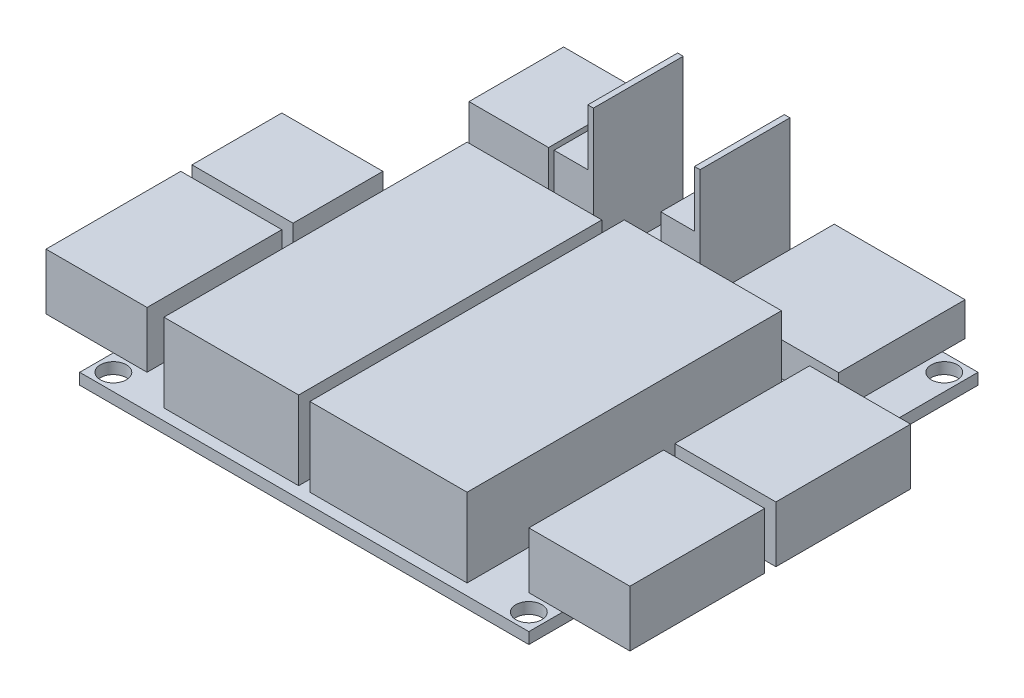
SolidWorks part; units mm, degrees
ref_plane "Front Plane" through (0, 0, 0) normal (0, 0, 1) x (1, 0, 0)
ref_plane "Top Plane" through (0, 0, 0) normal (0, 1, 0) x (1, 0, 0)
ref_plane "Right Plane" through (0, 0, 0) normal (1, 0, 0) x (0, 0, -1)
sketch "pcb layout" plane through (0, 0, 0) normal (0, 1, 0) x (1, 0, 0)
  line L0 (0, 0) -> (0, 50.8)
  line L1 (0, 50.8) -> (50.8, 50.8)
  line L2 (50.8, 50.8) -> (50.8, 0)
  line L3 (50.8, 0) -> (0, 0)
  line L4 (13.97, 38.1) -> (13.97, 36.83)
  line L5 (11.43, 38.735) -> (16.51, 38.735)
  line L6 (16.51, 38.735) -> (16.51, 36.195)
  line L7 (16.51, 36.195) -> (11.43, 36.195)
  line L8 (11.43, 36.195) -> (11.43, 38.735)
  line L9 (21.59, 44.45) -> (21.59, 45.72)
  line L10 (24.13, 43.815) -> (19.05, 43.815)
  line L11 (19.05, 43.815) -> (19.05, 46.355)
  line L12 (19.05, 46.355) -> (24.13, 46.355)
  line L13 (24.13, 46.355) -> (24.13, 43.815)
  line L14 (21.59, 47.625) -> (21.59, 48.895)
  line L15 (24.13, 46.99) -> (19.05, 46.99)
  line L16 (19.05, 46.99) -> (19.05, 49.53)
  line L17 (19.05, 49.53) -> (24.13, 49.53)
  line L18 (24.13, 49.53) -> (24.13, 46.99)
  line L19 (21.59, 40.3225) -> (21.59, 41.5925)
  line L20 (24.13, 39.6875) -> (19.05, 39.6875)
  line L21 (19.05, 39.6875) -> (19.05, 42.2275)
  line L22 (19.05, 42.2275) -> (24.13, 42.2275)
  line L23 (24.13, 42.2275) -> (24.13, 39.6875)
  line L24 (21.59, 37.1475) -> (21.59, 38.4175)
  line L25 (24.13, 36.5125) -> (19.05, 36.5125)
  line L26 (19.05, 36.5125) -> (19.05, 39.0525)
  line L27 (19.05, 39.0525) -> (24.13, 39.0525)
  line L28 (24.13, 39.0525) -> (24.13, 36.5125)
  line L29 (13.208, 35.56) -> (17.272, 35.56)
  line L30 (13.208, 35.56) -> (13.208, 33.02)
  line L31 (17.272, 33.02) -> (13.208, 33.02)
  line L32 (17.272, 33.02) -> (17.272, 35.56)
  line L33 (15.875, 34.29) -> (15.24, 34.29)
  line L34 (14.224, 33.655) -> (14.224, 34.925)
  line L35 (14.224, 34.925) -> (15.24, 34.29)
  line L36 (15.24, 34.29) -> (13.716, 34.29)
  line L37 (15.24, 34.29) -> (14.224, 33.655)
  line L38 (15.24, 33.655) -> (15.24, 34.29)
  line L39 (15.24, 34.29) -> (15.24, 34.925)
  line L40 (4.39, 39.64) -> (6.49, 39.64)
  line L41 (4.39, 50.34) -> (4.39, 45.04)
  line L42 (4.39, 39.64) -> (4.39, 40.34)
  line L43 (13.39, 50.34) -> (13.39, 39.64)
  line L44 (13.39, 39.64) -> (11.29, 39.64)
  line L45 (13.39, 50.34) -> (4.39, 50.34)
  line L46 (8.255, 1.27) -> (23.495, 1.27)
  line L47 (23.495, 1.27) -> (23.495, 35.56)
  line L48 (23.495, 35.56) -> (8.255, 35.56)
  line L49 (8.255, 35.56) -> (8.255, 1.27)
  line L50 (12.2936, 3.8354) -> (11.7343, 3.8354)
  line L51 (11.7343, 3.8354) -> (11.7343, 4.115)
  line L52 (11.7343, 4.115) -> (11.8275, 4.2082)
  line L53 (11.8275, 4.2082) -> (12.014, 4.2082)
  line L54 (12.014, 4.2082) -> (12.1072, 4.115)
  line L55 (12.1072, 4.115) -> (12.1072, 3.8354)
  line L56 (12.1072, 4.0218) -> (12.2936, 4.2082)
  line L57 (11.7343, 4.3967) -> (12.2936, 4.7696)
  line L58 (11.7343, 4.7696) -> (12.2936, 4.3967)
  line L59 (14.8336, 4.0218) -> (14.2743, 4.0218)
  line L60 (14.2743, 3.8354) -> (14.2743, 4.2082)
  line L61 (14.2743, 4.3967) -> (14.8336, 4.7696)
  line L62 (14.2743, 4.7696) -> (14.8336, 4.3967)
  line L63 (16.9075, 4.2082) -> (16.8143, 4.115)
  line L64 (16.8143, 4.115) -> (16.8143, 3.9286)
  line L65 (16.8143, 3.9286) -> (16.9075, 3.8354)
  line L66 (16.9075, 3.8354) -> (17.2804, 3.8354)
  line L67 (17.2804, 3.8354) -> (17.3736, 3.9286)
  line L68 (17.3736, 3.9286) -> (17.3736, 4.115)
  line L69 (17.3736, 4.115) -> (17.2804, 4.2082)
  line L70 (17.2804, 4.2082) -> (17.094, 4.2082)
  line L71 (17.094, 4.2082) -> (17.094, 4.0218)
  line L72 (17.3736, 4.3967) -> (16.8143, 4.3967)
  line L73 (16.8143, 4.3967) -> (17.3736, 4.7696)
  line L74 (17.3736, 4.7696) -> (16.8143, 4.7696)
  line L75 (16.8143, 4.958) -> (17.3736, 4.958)
  line L76 (17.3736, 4.958) -> (17.3736, 5.2377)
  line L77 (17.3736, 5.2377) -> (17.2804, 5.3309)
  line L78 (17.2804, 5.3309) -> (16.9075, 5.3309)
  line L79 (16.9075, 5.3309) -> (16.8143, 5.2377)
  line L80 (16.8143, 5.2377) -> (16.8143, 4.958)
  line L81 (19.3543, 3.8354) -> (19.7272, 3.8354)
  line L82 (19.7272, 3.8354) -> (19.9136, 4.0218)
  line L83 (19.9136, 4.0218) -> (19.7272, 4.2082)
  line L84 (19.7272, 4.2082) -> (19.3543, 4.2082)
  line L85 (19.4475, 4.7696) -> (19.3543, 4.6763)
  line L86 (19.3543, 4.6763) -> (19.3543, 4.4899)
  line L87 (19.3543, 4.4899) -> (19.4475, 4.3967)
  line L88 (19.4475, 4.3967) -> (19.8204, 4.3967)
  line L89 (19.8204, 4.3967) -> (19.9136, 4.4899)
  line L90 (19.9136, 4.4899) -> (19.9136, 4.6763)
  line L91 (19.9136, 4.6763) -> (19.8204, 4.7696)
  line L92 (19.4475, 5.3309) -> (19.3543, 5.2377)
  line L93 (19.3543, 5.2377) -> (19.3543, 5.0512)
  line L94 (19.3543, 5.0512) -> (19.4475, 4.958)
  line L95 (19.4475, 4.958) -> (19.8204, 4.958)
  line L96 (19.8204, 4.958) -> (19.9136, 5.0512)
  line L97 (19.9136, 5.0512) -> (19.9136, 5.2377)
  line L98 (19.9136, 5.2377) -> (19.8204, 5.3309)
  line L99 (21.8943, 3.8354) -> (22.4536, 3.8354)
  line L100 (22.2672, 3.8354) -> (21.8943, 4.2082)
  line L101 (22.174, 3.9286) -> (22.4536, 4.2082)
  line L102 (21.8943, 4.7696) -> (21.8943, 4.3967)
  line L103 (21.8943, 4.3967) -> (22.4536, 4.3967)
  line L104 (22.4536, 4.3967) -> (22.4536, 4.7696)
  line L105 (22.174, 4.3967) -> (22.174, 4.5831)
  line L106 (21.8943, 4.958) -> (21.9875, 4.958)
  line L107 (21.9875, 4.958) -> (22.174, 5.1444)
  line L108 (22.174, 5.1444) -> (21.9875, 5.3309)
  line L109 (21.9875, 5.3309) -> (21.8943, 5.3309)
  line L110 (22.174, 5.1444) -> (22.4536, 5.1444)
  line L111 (9.2875, 4.2082) -> (9.1943, 4.115)
  line L112 (9.1943, 4.115) -> (9.1943, 3.9286)
  line L113 (9.1943, 3.9286) -> (9.2875, 3.8354)
  line L114 (9.2875, 3.8354) -> (9.3808, 3.8354)
  line L115 (9.3808, 3.8354) -> (9.474, 3.9286)
  line L116 (9.474, 3.9286) -> (9.474, 4.115)
  line L117 (9.474, 4.115) -> (9.5672, 4.2082)
  line L118 (9.5672, 4.2082) -> (9.6604, 4.2082)
  line L119 (9.6604, 4.2082) -> (9.7536, 4.115)
  line L120 (9.7536, 4.115) -> (9.7536, 3.9286)
  line L121 (9.7536, 3.9286) -> (9.6604, 3.8354)
  line L122 (9.7536, 4.5831) -> (9.1943, 4.5831)
  line L123 (9.1943, 4.3967) -> (9.1943, 4.7696)
  line L124 (9.7536, 4.958) -> (9.3808, 4.958)
  line L125 (9.3808, 4.958) -> (9.1943, 5.1444)
  line L126 (9.1943, 5.1444) -> (9.3808, 5.3309)
  line L127 (9.3808, 5.3309) -> (9.7536, 5.3309)
  line L128 (9.474, 4.958) -> (9.474, 5.3309)
  line L129 (9.7536, 5.7058) -> (9.1943, 5.7058)
  line L130 (9.1943, 5.5193) -> (9.1943, 5.8922)
  line L131 (9.1943, 6.4535) -> (9.1943, 6.0806)
  line L132 (9.1943, 6.0806) -> (9.7536, 6.0806)
  line L133 (9.7536, 6.0806) -> (9.7536, 6.4535)
  line L134 (9.474, 6.0806) -> (9.474, 6.2671)
  line L135 (7.62, 36.5125) -> (7.62, 32.0675)
  line L136 (7.62, 32.0675) -> (5.715, 32.0675)
  line L137 (5.715, 32.0675) -> (5.715, 36.5125)
  line L138 (5.715, 36.5125) -> (7.62, 36.5125)
  line L139 (12.7, 32.512) -> (17.78, 32.512)
  line L140 (17.78, 32.512) -> (17.78, 31.75)
  line L141 (17.78, 31.75) -> (17.78, 30.988)
  line L142 (17.78, 30.988) -> (12.7, 30.988)
  line L143 (12.7, 30.988) -> (12.7, 31.75)
  line L144 (12.7, 31.75) -> (12.7, 32.512)
  line L145 (17.78, 31.75) -> (18.034, 31.75)
  line L146 (12.7, 31.75) -> (12.446, 31.75)
  line L147 (13.2842, 32.0214) -> (13.5723, 32.3095)
  line L148 (13.5723, 32.3095) -> (13.5723, 31.4452)
  line L149 (13.2842, 31.4452) -> (13.8604, 31.4452)
  line L150 (14.2197, 31.4452) -> (14.2197, 31.5893)
  line L151 (14.2197, 31.5893) -> (14.3638, 31.5893)
  line L152 (14.3638, 31.5893) -> (14.3638, 31.4452)
  line L153 (14.3638, 31.4452) -> (14.2197, 31.4452)
  line L154 (14.6875, 32.0214) -> (14.9756, 32.3095)
  line L155 (14.9756, 32.3095) -> (14.9756, 31.4452)
  line L156 (14.6875, 31.4452) -> (15.2637, 31.4452)
  line L157 (15.623, 32.3095) -> (15.623, 31.4452)
  line L158 (15.623, 31.7333) -> (16.1992, 32.3095)
  line L159 (15.7671, 31.8774) -> (16.1992, 31.4452)
  line L160 (16.5585, 31.4452) -> (16.7026, 31.4452)
  line L161 (16.7026, 31.4452) -> (16.7026, 31.7333)
  line L162 (16.7026, 31.7333) -> (16.5585, 31.8774)
  line L163 (16.5585, 31.8774) -> (16.5585, 32.1655)
  line L164 (16.5585, 32.1655) -> (16.7026, 32.3095)
  line L165 (16.7026, 32.3095) -> (16.9907, 32.3095)
  line L166 (16.9907, 32.3095) -> (17.1347, 32.1655)
  line L167 (17.1347, 32.1655) -> (17.1347, 31.8774)
  line L168 (17.1347, 31.8774) -> (16.9907, 31.7333)
  line L169 (16.9907, 31.7333) -> (16.9907, 31.4452)
  line L170 (16.9907, 31.4452) -> (17.1347, 31.4452)
  line L171 (12.7, 12.192) -> (17.78, 12.192)
  line L172 (17.78, 12.192) -> (17.78, 11.43)
  line L173 (17.78, 11.43) -> (17.78, 10.668)
  line L174 (17.78, 10.668) -> (12.7, 10.668)
  line L175 (12.7, 10.668) -> (12.7, 11.43)
  line L176 (12.7, 11.43) -> (12.7, 12.192)
  line L177 (17.78, 11.43) -> (18.034, 11.43)
  line L178 (12.7, 11.43) -> (12.446, 11.43)
  line L179 (13.2842, 11.7014) -> (13.5723, 11.9895)
  line L180 (13.5723, 11.9895) -> (13.5723, 11.1252)
  line L181 (13.2842, 11.1252) -> (13.8604, 11.1252)
  line L182 (14.2197, 11.2693) -> (14.2197, 11.8455)
  line L183 (14.2197, 11.8455) -> (14.3638, 11.9895)
  line L184 (14.3638, 11.9895) -> (14.6519, 11.9895)
  line L185 (14.6519, 11.9895) -> (14.7959, 11.8455)
  line L186 (14.7959, 11.8455) -> (14.7959, 11.2693)
  line L187 (14.7959, 11.2693) -> (14.6519, 11.1252)
  line L188 (14.6519, 11.1252) -> (14.3638, 11.1252)
  line L189 (14.3638, 11.1252) -> (14.2197, 11.2693)
  line L190 (14.2197, 11.2693) -> (14.7959, 11.8455)
  line L191 (15.1552, 11.9895) -> (15.1552, 11.1252)
  line L192 (15.1552, 11.4133) -> (15.7315, 11.9895)
  line L193 (15.2993, 11.5574) -> (15.7315, 11.1252)
  line L194 (16.0907, 11.1252) -> (16.2348, 11.1252)
  line L195 (16.2348, 11.1252) -> (16.2348, 11.4133)
  line L196 (16.2348, 11.4133) -> (16.0907, 11.5574)
  line L197 (16.0907, 11.5574) -> (16.0907, 11.8455)
  line L198 (16.0907, 11.8455) -> (16.2348, 11.9895)
  line L199 (16.2348, 11.9895) -> (16.5229, 11.9895)
  line L200 (16.5229, 11.9895) -> (16.667, 11.8455)
  line L201 (16.667, 11.8455) -> (16.667, 11.5574)
  line L202 (16.667, 11.5574) -> (16.5229, 11.4133)
  line L203 (16.5229, 11.4133) -> (16.5229, 11.1252)
  line L204 (16.5229, 11.1252) -> (16.667, 11.1252)
  line L205 (12.7, 9.652) -> (17.78, 9.652)
  line L206 (17.78, 9.652) -> (17.78, 8.89)
  line L207 (17.78, 8.89) -> (17.78, 8.128)
  line L208 (17.78, 8.128) -> (12.7, 8.128)
  line L209 (12.7, 8.128) -> (12.7, 8.89)
  line L210 (12.7, 8.89) -> (12.7, 9.652)
  line L211 (17.78, 8.89) -> (18.034, 8.89)
  line L212 (12.7, 8.89) -> (12.446, 8.89)
  line L213 (13.2842, 9.1614) -> (13.5723, 9.4495)
  line L214 (13.5723, 9.4495) -> (13.5723, 8.5852)
  line L215 (13.2842, 8.5852) -> (13.8604, 8.5852)
  line L216 (14.2197, 8.7293) -> (14.2197, 9.3055)
  line L217 (14.2197, 9.3055) -> (14.3638, 9.4495)
  line L218 (14.3638, 9.4495) -> (14.6519, 9.4495)
  line L219 (14.6519, 9.4495) -> (14.7959, 9.3055)
  line L220 (14.7959, 9.3055) -> (14.7959, 8.7293)
  line L221 (14.7959, 8.7293) -> (14.6519, 8.5852)
  line L222 (14.6519, 8.5852) -> (14.3638, 8.5852)
  line L223 (14.3638, 8.5852) -> (14.2197, 8.7293)
  line L224 (14.2197, 8.7293) -> (14.7959, 9.3055)
  line L225 (15.1552, 8.7293) -> (15.1552, 9.3055)
  line L226 (15.1552, 9.3055) -> (15.2993, 9.4495)
  line L227 (15.2993, 9.4495) -> (15.5874, 9.4495)
  line L228 (15.5874, 9.4495) -> (15.7315, 9.3055)
  line L229 (15.7315, 9.3055) -> (15.7315, 8.7293)
  line L230 (15.7315, 8.7293) -> (15.5874, 8.5852)
  line L231 (15.5874, 8.5852) -> (15.2993, 8.5852)
  line L232 (15.2993, 8.5852) -> (15.1552, 8.7293)
  line L233 (15.1552, 8.7293) -> (15.7315, 9.3055)
  line L234 (16.0907, 8.5852) -> (16.2348, 8.5852)
  line L235 (16.2348, 8.5852) -> (16.2348, 8.8733)
  line L236 (16.2348, 8.8733) -> (16.0907, 9.0174)
  line L237 (16.0907, 9.0174) -> (16.0907, 9.3055)
  line L238 (16.0907, 9.3055) -> (16.2348, 9.4495)
  line L239 (16.2348, 9.4495) -> (16.5229, 9.4495)
  line L240 (16.5229, 9.4495) -> (16.667, 9.3055)
  line L241 (16.667, 9.3055) -> (16.667, 9.0174)
  line L242 (16.667, 9.0174) -> (16.5229, 8.8733)
  line L243 (16.5229, 8.8733) -> (16.5229, 8.5852)
  line L244 (16.5229, 8.5852) -> (16.667, 8.5852)
  line L245 (12.7, 7.112) -> (17.78, 7.112)
  line L246 (17.78, 7.112) -> (17.78, 6.35)
  line L247 (17.78, 6.35) -> (17.78, 5.588)
  line L248 (17.78, 5.588) -> (12.7, 5.588)
  line L249 (12.7, 5.588) -> (12.7, 6.35)
  line L250 (12.7, 6.35) -> (12.7, 7.112)
  line L251 (17.78, 6.35) -> (18.034, 6.35)
  line L252 (12.7, 6.35) -> (12.446, 6.35)
  line L253 (13.2842, 6.6214) -> (13.5723, 6.9095)
  line L254 (13.5723, 6.9095) -> (13.5723, 6.0452)
  line L255 (13.2842, 6.0452) -> (13.8604, 6.0452)
  line L256 (14.2197, 6.1893) -> (14.2197, 6.7655)
  line L257 (14.2197, 6.7655) -> (14.3638, 6.9095)
  line L258 (14.3638, 6.9095) -> (14.6519, 6.9095)
  line L259 (14.6519, 6.9095) -> (14.7959, 6.7655)
  line L260 (14.7959, 6.7655) -> (14.7959, 6.1893)
  line L261 (14.7959, 6.1893) -> (14.6519, 6.0452)
  line L262 (14.6519, 6.0452) -> (14.3638, 6.0452)
  line L263 (14.3638, 6.0452) -> (14.2197, 6.1893)
  line L264 (14.2197, 6.1893) -> (14.7959, 6.7655)
  line L265 (15.1552, 6.9095) -> (15.1552, 6.0452)
  line L266 (15.1552, 6.3333) -> (15.7315, 6.9095)
  line L267 (15.2993, 6.4774) -> (15.7315, 6.0452)
  line L268 (16.0907, 6.0452) -> (16.2348, 6.0452)
  line L269 (16.2348, 6.0452) -> (16.2348, 6.3333)
  line L270 (16.2348, 6.3333) -> (16.0907, 6.4774)
  line L271 (16.0907, 6.4774) -> (16.0907, 6.7655)
  line L272 (16.0907, 6.7655) -> (16.2348, 6.9095)
  line L273 (16.2348, 6.9095) -> (16.5229, 6.9095)
  line L274 (16.5229, 6.9095) -> (16.667, 6.7655)
  line L275 (16.667, 6.7655) -> (16.667, 6.4774)
  line L276 (16.667, 6.4774) -> (16.5229, 6.3333)
  line L277 (16.5229, 6.3333) -> (16.5229, 6.0452)
  line L278 (16.5229, 6.0452) -> (16.667, 6.0452)
  line L279 (17.78, 28.448) -> (12.7, 28.448)
  line L280 (12.7, 28.448) -> (12.7, 29.21)
  line L281 (12.7, 29.21) -> (12.7, 29.972)
  line L282 (12.7, 29.972) -> (17.78, 29.972)
  line L283 (17.78, 29.972) -> (17.78, 29.21)
  line L284 (17.78, 29.21) -> (17.78, 28.448)
  line L285 (12.7, 29.21) -> (12.446, 29.21)
  line L286 (17.78, 29.21) -> (18.034, 29.21)
  line L287 (13.6061, 29.2274) -> (13.8942, 29.5155)
  line L288 (13.8942, 29.5155) -> (13.8942, 28.6512)
  line L289 (13.6061, 28.6512) -> (14.1823, 28.6512)
  line L290 (14.5417, 28.7953) -> (14.5417, 29.3715)
  line L291 (14.5417, 29.3715) -> (14.6857, 29.5155)
  line L292 (14.6857, 29.5155) -> (14.9738, 29.5155)
  line L293 (14.9738, 29.5155) -> (15.1179, 29.3715)
  line L294 (15.1179, 29.3715) -> (15.1179, 28.7953)
  line L295 (15.1179, 28.7953) -> (14.9738, 28.6512)
  line L296 (14.9738, 28.6512) -> (14.6857, 28.6512)
  line L297 (14.6857, 28.6512) -> (14.5417, 28.7953)
  line L298 (14.5417, 28.7953) -> (15.1179, 29.3715)
  line L299 (15.4772, 29.5155) -> (15.4772, 28.6512)
  line L300 (15.4772, 28.9393) -> (16.0534, 29.5155)
  line L301 (15.6212, 29.0834) -> (16.0534, 28.6512)
  line L302 (16.4127, 28.6512) -> (16.5567, 28.6512)
  line L303 (16.5567, 28.6512) -> (16.5567, 28.9393)
  line L304 (16.5567, 28.9393) -> (16.4127, 29.0834)
  line L305 (16.4127, 29.0834) -> (16.4127, 29.3715)
  line L306 (16.4127, 29.3715) -> (16.5567, 29.5155)
  line L307 (16.5567, 29.5155) -> (16.8448, 29.5155)
  line L308 (16.8448, 29.5155) -> (16.9889, 29.3715)
  line L309 (16.9889, 29.3715) -> (16.9889, 29.0834)
  line L310 (16.9889, 29.0834) -> (16.8448, 28.9393)
  line L311 (16.8448, 28.9393) -> (16.8448, 28.6512)
  line L312 (16.8448, 28.6512) -> (16.9889, 28.6512)
  line L313 (17.78, 25.908) -> (12.7, 25.908)
  line L314 (12.7, 25.908) -> (12.7, 26.67)
  line L315 (12.7, 26.67) -> (12.7, 27.432)
  line L316 (12.7, 27.432) -> (17.78, 27.432)
  line L317 (17.78, 27.432) -> (17.78, 26.67)
  line L318 (17.78, 26.67) -> (17.78, 25.908)
  line L319 (12.7, 26.67) -> (12.446, 26.67)
  line L320 (17.78, 26.67) -> (18.034, 26.67)
  line L321 (13.6061, 26.6874) -> (13.8942, 26.9755)
  line L322 (13.8942, 26.9755) -> (13.8942, 26.1112)
  line L323 (13.6061, 26.1112) -> (14.1823, 26.1112)
  line L324 (14.5417, 26.2553) -> (14.5417, 26.8315)
  line L325 (14.5417, 26.8315) -> (14.6857, 26.9755)
  line L326 (14.6857, 26.9755) -> (14.9738, 26.9755)
  line L327 (14.9738, 26.9755) -> (15.1179, 26.8315)
  line L328 (15.1179, 26.8315) -> (15.1179, 26.2553)
  line L329 (15.1179, 26.2553) -> (14.9738, 26.1112)
  line L330 (14.9738, 26.1112) -> (14.6857, 26.1112)
  line L331 (14.6857, 26.1112) -> (14.5417, 26.2553)
  line L332 (14.5417, 26.2553) -> (15.1179, 26.8315)
  line L333 (15.4772, 26.2553) -> (15.4772, 26.8315)
  line L334 (15.4772, 26.8315) -> (15.6212, 26.9755)
  line L335 (15.6212, 26.9755) -> (15.9093, 26.9755)
  line L336 (15.9093, 26.9755) -> (16.0534, 26.8315)
  line L337 (16.0534, 26.8315) -> (16.0534, 26.2553)
  line L338 (16.0534, 26.2553) -> (15.9093, 26.1112)
  line L339 (15.9093, 26.1112) -> (15.6212, 26.1112)
  line L340 (15.6212, 26.1112) -> (15.4772, 26.2553)
  line L341 (15.4772, 26.2553) -> (16.0534, 26.8315)
  line L342 (16.4127, 26.1112) -> (16.5567, 26.1112)
  line L343 (16.5567, 26.1112) -> (16.5567, 26.3993)
  line L344 (16.5567, 26.3993) -> (16.4127, 26.5434)
  line L345 (16.4127, 26.5434) -> (16.4127, 26.8315)
  line L346 (16.4127, 26.8315) -> (16.5567, 26.9755)
  line L347 (16.5567, 26.9755) -> (16.8448, 26.9755)
  line L348 (16.8448, 26.9755) -> (16.9889, 26.8315)
  line L349 (16.9889, 26.8315) -> (16.9889, 26.5434)
  line L350 (16.9889, 26.5434) -> (16.8448, 26.3993)
  line L351 (16.8448, 26.3993) -> (16.8448, 26.1112)
  line L352 (16.8448, 26.1112) -> (16.9889, 26.1112)
  line L353 (17.78, 23.368) -> (12.7, 23.368)
  line L354 (12.7, 23.368) -> (12.7, 24.13)
  line L355 (12.7, 24.13) -> (12.7, 24.892)
  line L356 (12.7, 24.892) -> (17.78, 24.892)
  line L357 (17.78, 24.892) -> (17.78, 24.13)
  line L358 (17.78, 24.13) -> (17.78, 23.368)
  line L359 (12.7, 24.13) -> (12.446, 24.13)
  line L360 (17.78, 24.13) -> (18.034, 24.13)
  line L361 (13.6061, 24.1474) -> (13.8942, 24.4355)
  line L362 (13.8942, 24.4355) -> (13.8942, 23.5712)
  line L363 (13.6061, 23.5712) -> (14.1823, 23.5712)
  line L364 (14.5417, 23.7153) -> (14.5417, 24.2915)
  line L365 (14.5417, 24.2915) -> (14.6857, 24.4355)
  line L366 (14.6857, 24.4355) -> (14.9738, 24.4355)
  line L367 (14.9738, 24.4355) -> (15.1179, 24.2915)
  line L368 (15.1179, 24.2915) -> (15.1179, 23.7153)
  line L369 (15.1179, 23.7153) -> (14.9738, 23.5712)
  line L370 (14.9738, 23.5712) -> (14.6857, 23.5712)
  line L371 (14.6857, 23.5712) -> (14.5417, 23.7153)
  line L372 (14.5417, 23.7153) -> (15.1179, 24.2915)
  line L373 (15.4772, 24.4355) -> (15.4772, 23.5712)
  line L374 (15.4772, 23.8593) -> (16.0534, 24.4355)
  line L375 (15.6212, 24.0034) -> (16.0534, 23.5712)
  line L376 (16.4127, 23.5712) -> (16.5567, 23.5712)
  line L377 (16.5567, 23.5712) -> (16.5567, 23.8593)
  line L378 (16.5567, 23.8593) -> (16.4127, 24.0034)
  line L379 (16.4127, 24.0034) -> (16.4127, 24.2915)
  line L380 (16.4127, 24.2915) -> (16.5567, 24.4355)
  line L381 (16.5567, 24.4355) -> (16.8448, 24.4355)
  line L382 (16.8448, 24.4355) -> (16.9889, 24.2915)
  line L383 (16.9889, 24.2915) -> (16.9889, 24.0034)
  line L384 (16.9889, 24.0034) -> (16.8448, 23.8593)
  line L385 (16.8448, 23.8593) -> (16.8448, 23.5712)
  line L386 (16.8448, 23.5712) -> (16.9889, 23.5712)
  line L387 (17.78, 19.558) -> (12.7, 19.558)
  line L388 (12.7, 19.558) -> (12.7, 20.32)
  line L389 (12.7, 20.32) -> (12.7, 21.082)
  line L390 (12.7, 21.082) -> (17.78, 21.082)
  line L391 (17.78, 21.082) -> (17.78, 20.32)
  line L392 (17.78, 20.32) -> (17.78, 19.558)
  line L393 (12.7, 20.32) -> (12.446, 20.32)
  line L394 (17.78, 20.32) -> (18.034, 20.32)
  line L395 (13.6061, 20.3374) -> (13.8942, 20.6255)
  line L396 (13.8942, 20.6255) -> (13.8942, 19.7612)
  line L397 (13.6061, 19.7612) -> (14.1823, 19.7612)
  line L398 (14.5417, 19.9053) -> (14.5417, 20.4815)
  line L399 (14.5417, 20.4815) -> (14.6857, 20.6255)
  line L400 (14.6857, 20.6255) -> (14.9738, 20.6255)
  line L401 (14.9738, 20.6255) -> (15.1179, 20.4815)
  line L402 (15.1179, 20.4815) -> (15.1179, 19.9053)
  line L403 (15.1179, 19.9053) -> (14.9738, 19.7612)
  line L404 (14.9738, 19.7612) -> (14.6857, 19.7612)
  line L405 (14.6857, 19.7612) -> (14.5417, 19.9053)
  line L406 (14.5417, 19.9053) -> (15.1179, 20.4815)
  line L407 (15.4772, 20.6255) -> (15.4772, 19.7612)
  line L408 (15.4772, 20.0493) -> (16.0534, 20.6255)
  line L409 (15.6212, 20.1934) -> (16.0534, 19.7612)
  line L410 (16.4127, 19.7612) -> (16.5567, 19.7612)
  line L411 (16.5567, 19.7612) -> (16.5567, 20.0493)
  line L412 (16.5567, 20.0493) -> (16.4127, 20.1934)
  line L413 (16.4127, 20.1934) -> (16.4127, 20.4815)
  line L414 (16.4127, 20.4815) -> (16.5567, 20.6255)
  line L415 (16.5567, 20.6255) -> (16.8448, 20.6255)
  line L416 (16.8448, 20.6255) -> (16.9889, 20.4815)
  line L417 (16.9889, 20.4815) -> (16.9889, 20.1934)
  line L418 (16.9889, 20.1934) -> (16.8448, 20.0493)
  line L419 (16.8448, 20.0493) -> (16.8448, 19.7612)
  line L420 (16.8448, 19.7612) -> (16.9889, 19.7612)
  line L421 (17.78, 17.018) -> (12.7, 17.018)
  line L422 (12.7, 17.018) -> (12.7, 17.78)
  line L423 (12.7, 17.78) -> (12.7, 18.542)
  line L424 (12.7, 18.542) -> (17.78, 18.542)
  line L425 (17.78, 18.542) -> (17.78, 17.78)
  line L426 (17.78, 17.78) -> (17.78, 17.018)
  line L427 (12.7, 17.78) -> (12.446, 17.78)
  line L428 (17.78, 17.78) -> (18.034, 17.78)
  line L429 (13.6061, 17.7974) -> (13.8942, 18.0855)
  line L430 (13.8942, 18.0855) -> (13.8942, 17.2212)
  line L431 (13.6061, 17.2212) -> (14.1823, 17.2212)
  line L432 (14.5417, 17.3653) -> (14.5417, 17.9415)
  line L433 (14.5417, 17.9415) -> (14.6857, 18.0855)
  line L434 (14.6857, 18.0855) -> (14.9738, 18.0855)
  line L435 (14.9738, 18.0855) -> (15.1179, 17.9415)
  line L436 (15.1179, 17.9415) -> (15.1179, 17.3653)
  line L437 (15.1179, 17.3653) -> (14.9738, 17.2212)
  line L438 (14.9738, 17.2212) -> (14.6857, 17.2212)
  line L439 (14.6857, 17.2212) -> (14.5417, 17.3653)
  line L440 (14.5417, 17.3653) -> (15.1179, 17.9415)
  line L441 (15.4772, 17.3653) -> (15.4772, 17.9415)
  line L442 (15.4772, 17.9415) -> (15.6212, 18.0855)
  line L443 (15.6212, 18.0855) -> (15.9093, 18.0855)
  line L444 (15.9093, 18.0855) -> (16.0534, 17.9415)
  line L445 (16.0534, 17.9415) -> (16.0534, 17.3653)
  line L446 (16.0534, 17.3653) -> (15.9093, 17.2212)
  line L447 (15.9093, 17.2212) -> (15.6212, 17.2212)
  line L448 (15.6212, 17.2212) -> (15.4772, 17.3653)
  line L449 (15.4772, 17.3653) -> (16.0534, 17.9415)
  line L450 (16.4127, 17.2212) -> (16.5567, 17.2212)
  line L451 (16.5567, 17.2212) -> (16.5567, 17.5093)
  line L452 (16.5567, 17.5093) -> (16.4127, 17.6534)
  line L453 (16.4127, 17.6534) -> (16.4127, 17.9415)
  line L454 (16.4127, 17.9415) -> (16.5567, 18.0855)
  line L455 (16.5567, 18.0855) -> (16.8448, 18.0855)
  line L456 (16.8448, 18.0855) -> (16.9889, 17.9415)
  line L457 (16.9889, 17.9415) -> (16.9889, 17.6534)
  line L458 (16.9889, 17.6534) -> (16.8448, 17.5093)
  line L459 (16.8448, 17.5093) -> (16.8448, 17.2212)
  line L460 (16.8448, 17.2212) -> (16.9889, 17.2212)
  line L461 (17.78, 14.478) -> (12.7, 14.478)
  line L462 (12.7, 14.478) -> (12.7, 15.24)
  line L463 (12.7, 15.24) -> (12.7, 16.002)
  line L464 (12.7, 16.002) -> (17.78, 16.002)
  line L465 (17.78, 16.002) -> (17.78, 15.24)
  line L466 (17.78, 15.24) -> (17.78, 14.478)
  line L467 (12.7, 15.24) -> (12.446, 15.24)
  line L468 (17.78, 15.24) -> (18.034, 15.24)
  line L469 (13.6061, 15.2574) -> (13.8942, 15.5455)
  line L470 (13.8942, 15.5455) -> (13.8942, 14.6812)
  line L471 (13.6061, 14.6812) -> (14.1823, 14.6812)
  line L472 (14.5417, 14.8253) -> (14.5417, 15.4015)
  line L473 (14.5417, 15.4015) -> (14.6857, 15.5455)
  line L474 (14.6857, 15.5455) -> (14.9738, 15.5455)
  line L475 (14.9738, 15.5455) -> (15.1179, 15.4015)
  line L476 (15.1179, 15.4015) -> (15.1179, 14.8253)
  line L477 (15.1179, 14.8253) -> (14.9738, 14.6812)
  line L478 (14.9738, 14.6812) -> (14.6857, 14.6812)
  line L479 (14.6857, 14.6812) -> (14.5417, 14.8253)
  line L480 (14.5417, 14.8253) -> (15.1179, 15.4015)
  line L481 (15.4772, 15.5455) -> (15.4772, 14.6812)
  line L482 (15.4772, 14.9693) -> (16.0534, 15.5455)
  line L483 (15.6212, 15.1134) -> (16.0534, 14.6812)
  line L484 (16.4127, 14.6812) -> (16.5567, 14.6812)
  line L485 (16.5567, 14.6812) -> (16.5567, 14.9693)
  line L486 (16.5567, 14.9693) -> (16.4127, 15.1134)
  line L487 (16.4127, 15.1134) -> (16.4127, 15.4015)
  line L488 (16.4127, 15.4015) -> (16.5567, 15.5455)
  line L489 (16.5567, 15.5455) -> (16.8448, 15.5455)
  line L490 (16.8448, 15.5455) -> (16.9889, 15.4015)
  line L491 (16.9889, 15.4015) -> (16.9889, 15.1134)
  line L492 (16.9889, 15.1134) -> (16.8448, 14.9693)
  line L493 (16.8448, 14.9693) -> (16.8448, 14.6812)
  line L494 (16.8448, 14.6812) -> (16.9889, 14.6812)
  line L495 (6.35, 20.32) -> (6.35, 30.48)
  line L496 (-7.62, 20.32) -> (3.81, 20.32)
  line L497 (3.81, 20.32) -> (3.81, 30.48)
  line L498 (3.81, 30.48) -> (-7.62, 30.48)
  line L499 (-7.62, 30.48) -> (-7.62, 20.32)
  line L500 (34.925, 2.54) -> (32.385, 2.54)
  line L501 (32.385, 2.54) -> (32.385, 1.27)
  line L502 (32.385, 1.27) -> (24.765, 1.27)
  line L503 (24.765, 1.27) -> (24.765, 36.83)
  line L504 (24.765, 36.83) -> (42.545, 36.83)
  line L505 (42.545, 36.83) -> (42.545, 1.27)
  line L506 (42.545, 1.27) -> (34.925, 1.27)
  line L507 (34.925, 1.27) -> (34.925, 2.54)
  line L508 (46.77, 53.37) -> (31.97, 53.37)
  line L509 (31.97, 53.37) -> (31.97, 39.07)
  line L510 (31.97, 39.07) -> (46.77, 39.07)
  line L511 (46.77, 39.07) -> (46.77, 53.37)
  line L512 (44.45, 46.05) -> (43.18, 51.9)
  line L513 (43.18, 51.9) -> (41.91, 51.9)
  line L514 (41.91, 51.9) -> (40.64, 46.05)
  line L515 (38.1, 46.05) -> (36.83, 51.9)
  line L516 (36.83, 51.9) -> (35.56, 51.9)
  line L517 (35.56, 51.9) -> (34.29, 46.05)
  line L518 (13.97, 39.6875) -> (13.97, 49.8475)
  line L519 (13.97, 49.8475) -> (17.78, 49.8475)
  line L520 (17.78, 49.8475) -> (18.415, 49.8475)
  line L521 (18.415, 49.8475) -> (18.415, 39.6875)
  line L522 (18.415, 39.6875) -> (17.78, 39.6875)
  line L523 (17.78, 39.6875) -> (13.97, 39.6875)
  line L524 (17.78, 39.6875) -> (17.78, 49.8475)
  line L525 (26.035, 39.6875) -> (26.035, 49.8475)
  line L526 (26.035, 49.8475) -> (29.845, 49.8475)
  line L527 (29.845, 49.8475) -> (30.48, 49.8475)
  line L528 (30.48, 49.8475) -> (30.48, 39.6875)
  line L529 (30.48, 39.6875) -> (29.845, 39.6875)
  line L530 (29.845, 39.6875) -> (26.035, 39.6875)
  line L531 (29.845, 39.6875) -> (29.845, 49.8475)
  line L532 (6.35, 3.81) -> (6.35, 19.05)
  line L533 (3.81, 3.81) -> (-7.62, 3.81)
  line L534 (-7.62, 3.81) -> (-7.62, 19.05)
  line L535 (3.81, 19.05) -> (3.81, 3.81)
  line L536 (-7.62, 19.05) -> (3.81, 19.05)
  line L537 (44.45, 35.56) -> (44.45, 20.32)
  line L538 (46.99, 35.56) -> (58.42, 35.56)
  line L539 (58.42, 35.56) -> (58.42, 20.32)
  line L540 (46.99, 20.32) -> (46.99, 35.56)
  line L541 (58.42, 20.32) -> (46.99, 20.32)
  line L542 (49.2125, 40.9575) -> (49.2125, 36.5125)
  line L543 (49.2125, 36.5125) -> (47.3075, 36.5125)
  line L544 (47.3075, 36.5125) -> (47.3075, 40.9575)
  line L545 (47.3075, 40.9575) -> (49.2125, 40.9575)
  line L546 (44.45, 19.05) -> (44.45, 3.81)
  line L547 (46.99, 19.05) -> (58.42, 19.05)
  line L548 (58.42, 19.05) -> (58.42, 3.81)
  line L549 (46.99, 3.81) -> (46.99, 19.05)
  line L550 (58.42, 3.81) -> (46.99, 3.81)
  circle A0 centre (48.895, 1.905) radius 1.4732
  circle A1 centre (48.895, 48.895) radius 1.4732
  circle A2 centre (1.905, 48.895) radius 1.4732
  circle A3 centre (1.905, 1.905) radius 1.4732
  arc A4 (1.6542, 35.5301) -> (1.016, 34.29) centre (2.54, 34.29) ccw
  arc A5 (1.016, 34.29) -> (1.6256, 33.0708) centre (2.54, 34.29) ccw
  arc A6 (4.064, 34.29) -> (3.4756, 35.493) centre (2.54, 34.29) ccw
  arc A7 (3.4756, 33.087) -> (4.064, 34.29) centre (2.54, 34.29) ccw
  arc A8 (1.2391, 35.851) -> (0.508, 34.29) centre (2.54, 34.29) ccw
  arc A9 (0.508, 34.29) -> (1.5838, 32.4971) centre (2.54, 34.2901) ccw
  arc A10 (4.572, 34.29) -> (3.8526, 35.8412) centre (2.54, 34.29) ccw
  arc A11 (3.5482, 32.5257) -> (4.572, 34.29) centre (2.54, 34.2899) ccw
  circle A12 centre (45.94, 43.18) radius 1.15
  circle A13 centre (32.8, 43.18) radius 1.15
sketch "Sketch5" plane through (0, 0, 0) normal (0, 1, 0) x (1, 0, 0)
  line L0 (0, 50.8) -> (50.8, 50.8)
  line L1 (50.8, 50.8) -> (50.8, 0)
  line L2 (50.8, 0) -> (0, 0)
  line L3 (0, 0) -> (0, 50.8)
extrude "Boss-Extrude1" add sketch "Sketch5" against normal blind 1.27
sketch "Sketch6" plane through (0, 0, 0) normal (0, 1, 0) x (1, 0, 0)
  line L1 (-7.62, 30.48) -> (3.81, 30.48)
  line L2 (-7.62, 30.48) -> (-7.62, 20.32)
  line L3 (-7.62, 20.32) -> (3.81, 20.32)
  line L4 (3.81, 30.48) -> (3.81, 20.32)
  line L5 (-7.62, 19.05) -> (3.81, 19.05)
  line L6 (-7.62, 19.05) -> (-7.62, 3.81)
  line L7 (-7.62, 3.81) -> (3.81, 3.81)
  line L8 (3.81, 19.05) -> (3.81, 3.81)
  line L9 (46.99, 35.56) -> (58.42, 35.56)
  line L10 (46.99, 35.56) -> (46.99, 20.32)
  line L11 (46.99, 20.32) -> (58.42, 20.32)
  line L12 (58.42, 35.56) -> (58.42, 20.32)
  line L13 (46.99, 19.05) -> (58.42, 19.05)
  line L14 (46.99, 19.05) -> (46.99, 3.81)
  line L15 (46.99, 3.81) -> (58.42, 3.81)
  line L16 (58.42, 19.05) -> (58.42, 3.81)
extrude "Boss-Extrude2" add sketch "Sketch6" along normal blind 6.35
sketch "Sketch7" plane through (0, 0, 0) normal (0, 1, 0) x (1, 0, 0)
  line L1 (8.255, 35.56) -> (23.495, 35.56)
  line L2 (8.255, 35.56) -> (8.255, 1.27)
  line L3 (8.255, 1.27) -> (23.495, 1.27)
  line L4 (23.495, 35.56) -> (23.495, 1.27)
  line L5 (24.765, 36.83) -> (42.545, 36.83)
  line L6 (24.765, 36.83) -> (24.765, 1.27)
  line L7 (24.765, 1.27) -> (42.545, 1.27)
  line L8 (42.545, 36.83) -> (42.545, 1.27)
extrude "Boss-Extrude3" add sketch "Sketch7" along normal blind 8.89
sketch "Sketch8" plane through (0, 0, 0) normal (0, 1, 0) x (1, 0, 0)
  circle A0 centre (1.905, 48.895) radius 1.4732
  circle A1 centre (48.895, 48.895) radius 1.4732
  circle A2 centre (48.895, 1.905) radius 1.4732
  circle A3 centre (1.905, 1.905) radius 1.4732
  circle A4 centre (1.905, 48.895) radius 1.4732
  dimension "D1" = 2.9464
  dimension "D2" = 2.9464
  dimension "D3" = 2.9464
  dimension "D4" = 2.9464
extrude "Cut-Extrude1" cut sketch "Sketch8" against normal through all contours A0 | A1 | A3 | A2
sketch "Sketch9" plane through (0, 0, 0) normal (0, 1, 0) x (1, 0, 0)
  line L1 (30.48, 39.6875) -> (26.035, 39.6875)
  line L2 (30.48, 39.6875) -> (30.48, 49.8475)
  line L3 (30.48, 49.8475) -> (26.035, 49.8475)
  line L4 (26.035, 39.6875) -> (26.035, 49.8475)
  line L5 (30.48, 39.6875) -> (29.845, 39.6875)
  line L6 (30.48, 39.6875) -> (30.48, 49.8475)
  line L7 (30.48, 49.8475) -> (29.845, 49.8475)
  line L9 (18.415, 39.6875) -> (13.97, 39.6875)
  line L10 (18.415, 39.6875) -> (18.415, 49.8475)
  line L11 (18.415, 49.8475) -> (13.97, 49.8475)
  line L12 (13.97, 39.6875) -> (13.97, 49.8475)
  line L13 (18.415, 39.6875) -> (17.78, 39.6875)
  line L14 (18.415, 39.6875) -> (18.415, 49.8475)
  line L15 (18.415, 49.8475) -> (17.78, 49.8475)
extrude "Boss-Extrude4" add sketch "Sketch9" along normal blind 8.89
sketch "Sketch11" plane through (0, 8.89, 0) normal (0, 1, 0) x (1, 0, 0)
  line L0 (29.845, 39.6875) -> (29.845, 49.8475) construction
  line L1 (29.845, 39.6875) -> (29.845, 49.8475)
  line L2 (17.78, 39.6875) -> (17.78, 49.8475) construction
  line L3 (17.78, 39.6875) -> (17.78, 49.8475)
  line L4 (30.48, 49.8475) -> (30.48, 39.6875) construction
  line L5 (30.48, 49.8475) -> (30.48, 39.6875)
  line L6 (30.48, 39.6875) -> (29.845, 39.6875) construction
  line L7 (30.48, 39.6875) -> (29.845, 39.6875)
  line L8 (29.845, 49.8475) -> (30.48, 49.8475) construction
  line L9 (29.845, 49.8475) -> (30.48, 49.8475)
  line L10 (18.415, 49.8475) -> (18.415, 39.6875) construction
  line L11 (18.415, 49.8475) -> (18.415, 39.6875)
  line L12 (18.415, 39.6875) -> (17.78, 39.6875) construction
  line L13 (17.78, 49.8475) -> (18.415, 49.8475) construction
  line L14 (18.415, 39.6875) -> (17.78, 39.6875)
  line L15 (17.78, 49.8475) -> (18.415, 49.8475)
extrude "Boss-Extrude5" add sketch "Sketch11" along normal blind 6.35
sketch "Sketch12" plane through (0, 0, 0) normal (0, 1, 0) x (1, 0, 0)
  line L1 (4.39, 50.34) -> (13.39, 50.34)
  line L2 (4.39, 50.34) -> (4.39, 39.64)
  line L3 (4.39, 39.64) -> (13.39, 39.64)
  line L4 (13.39, 50.34) -> (13.39, 39.64)
extrude "Boss-Extrude6" add sketch "Sketch12" along normal blind 8.89
sketch "Sketch13" plane through (0, 0, 0) normal (0, 1, 0) x (1, 0, 0)
  line L1 (46.77, 39.07) -> (31.97, 39.07)
  line L2 (46.77, 39.07) -> (46.77, 53.37)
  line L3 (46.77, 53.37) -> (31.97, 53.37)
  line L4 (31.97, 39.07) -> (31.97, 53.37)
extrude "Boss-Extrude7" add sketch "Sketch13" along normal blind 3.81
sketch "Sketch16" plane through (0, 0, 0) normal (0, 1, 0) x (1, 0, 0)
  line L0 (21.59, 47.625) -> (21.59, 48.895) construction
  line L1 (21.59, 47.625) -> (21.59, 48.895) construction
  circle A0 centre (21.59, 48.26) radius 1.2166
sketch "Sketch17" plane through (0, 0, -50.34) normal (0, 0, -1) x (-1, 0, 0)
  line L0 (-8.89, 5.9162) -> (-4.39, 5.9162) construction
  line L1 (-4.39, 8.89) -> (-4.39, 0) construction
  line L2 (-8.89, 5.9162) -> (-13.39, 5.9162) construction
  line L3 (-13.39, 8.89) -> (-13.39, 0) construction
  circle A0 centre (-8.89, 5.9162) radius 2.5
  point P2 (-4.39, 5.9162)
  dimension "D1" = 5
extrude "Cut-Extrude2" cut sketch "Sketch17" against normal blind 6.35
